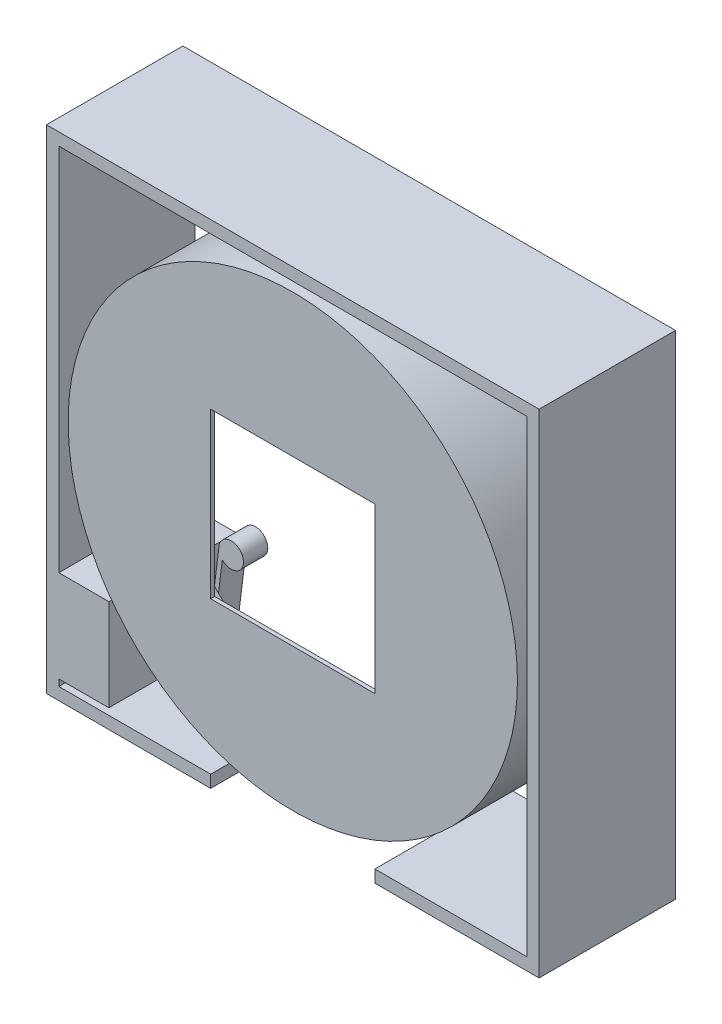
SolidWorks part; units mm, degrees
ref_plane "Front Plane" through (0, 0, 0) normal (0, 0, 1) x (1, 0, 0)
ref_plane "Top Plane" through (0, 0, 0) normal (0, 1, 0) x (1, 0, 0)
ref_plane "Right Plane" through (0, 0, 0) normal (1, 0, 0) x (0, 0, -1)
sketch "Sketch2" plane through (0, 0, 0) normal (0, 1, 0) x (1, 0, 0)
  line L0 (0, 0) -> (0, 14.0604) construction
  line L1 (0, 0) -> (43.434, 0)
  line L3 (0, 0) -> (0, 0.762)
  line L4 (43.434, 0) -> (43.434, 15.875)
  line L5 (0, 0.762) -> (42.672, 0.762)
  line L6 (42.672, 0.762) -> (42.672, 15.875)
  line L7 (42.672, 15.875) -> (43.434, 15.875)
  dimension "D1" = 15.875
  dimension "D2" = 86.868
  dimension "D3" = 0.762
revolve "Revolve1" add sketch "Sketch2" angle 360 about L0
sketch "Sketch3" plane through (0, 0, -0.762) normal (0, 0, -1) x (-1, 0, 0)
  line L1 (-15.875, -15.875) -> (15.875, -15.875)
  line L2 (-15.875, -15.875) -> (-15.875, 15.875)
  line L3 (-15.875, 15.875) -> (15.875, 15.875)
  line L4 (15.875, -15.875) -> (15.875, 15.875)
  line L5 (-15.875, -15.875) -> (15.875, 15.875) construction
  line L6 (-15.875, 15.875) -> (15.875, -15.875) construction
  point P0 (0, 0)
  dimension "D1" = 31.75
extrude "Cut-Extrude1" cut sketch "Sketch3" against normal through all contours L3 L4 L1 L2
sketch "Sketch4" plane through (0, 0, -0.762) normal (0, 0, -1) x (-1, 0, 0)
  line L1 (-12.7, 0) -> (12.7, 0)
  line L2 (-12.7, 0) -> (-12.7, -50.8)
  line L3 (-12.7, -50.8) -> (12.7, -50.8)
  line L4 (12.7, 0) -> (12.7, -50.8)
  point P4 (0, 0)
  dimension "D1" = 25.4
  dimension "D2" = 50.8
extrude "Cut-Extrude2" cut sketch "Sketch4" along normal through all contours L4 L3 L2 L1
sketch "Sketch5" plane through (0, 0, 0) normal (0, 0, 1) x (1, 0, 0)
  line L0 (45.2438, 45.2437) -> (-45.2437, 45.2437)
  line L1 (47.625, -47.625) -> (15.875, -47.625)
  line L2 (47.625, -47.625) -> (47.625, 47.625)
  line L3 (47.625, 47.625) -> (-47.625, 47.625)
  line L4 (-47.625, -47.625) -> (-47.625, 47.625)
  line L5 (47.625, -47.625) -> (-47.625, 47.625) construction
  line L6 (47.625, 47.625) -> (-47.625, -47.625) construction
  line L7 (-45.2437, -45.2438) -> (-45.2437, 45.2437)
  line L8 (45.2438, -45.2437) -> (15.875, -45.2437)
  line L9 (45.2438, -45.2437) -> (45.2438, 45.2437)
  line L10 (15.875, -45.2437) -> (15.875, -47.625)
  line L11 (0, 0) -> (0, -47.625) construction
  line L12 (-15.875, -45.2438) -> (-15.875, -47.625)
  line L13 (-15.875, -47.625) -> (-47.625, -47.625)
  line L14 (47.625, -47.625) -> (-47.625, -47.625) construction
  line L15 (-15.875, -45.2438) -> (-45.2437, -45.2438)
  line L16 (45.2438, -45.2437) -> (-45.2437, -45.2438) construction
  point P0 (0, 0)
  dimension "D2" = 95.25
  dimension "D3" = 31.75
  dimension "D1" = 2.3813
extrude "Boss-Extrude2" add sketch "Sketch5" against normal blind 26.3769 separate body contours L3 L4 L13 L12 L15 L7 L0 L9 L8 L10 L1 L2
sketch "Sketch6" plane through (0, 0, -26.3769) normal (0, 0, -1) x (-1, 0, 0)
  line L0 (34.8297, -43.9738) -> (32.7659, -27.3581)
  line L1 (34.8297, -26.1938) -> (44.9897, -26.1938)
  line L2 (34.8297, -26.1938) -> (34.8297, -43.9738)
  line L3 (34.8297, -43.9738) -> (44.9897, -43.9738)
  line L4 (44.9897, -26.1938) -> (44.9897, -43.9738)
  line L5 (33.4368, -25.7013) -> (34.8297, -36.9158)
  line L6 (45.2437, -45.2438) -> (45.2437, 45.2437) construction
  line L7 (15.875, -45.2438) -> (45.2437, -45.2438) construction
  circle A0 centre (31.0555, -25.7013) radius 2.3812
  dimension "D4" = 4.7625
  dimension "D1" = 17.78
  dimension "D2" = 10.16
  dimension "D3" = 0.87
  dimension "D5" = 0.254
  dimension "D6" = 1.27
extrude "Boss-Extrude3" add sketch "Sketch6" against normal blind 4.699 from offset 2.54 separate body contours L4 L1 L2 L3 | A0 | A0 L0 L2 L5 offset against normal yes
sketch "Sketch7" plane through (0, 0, -19.1379) normal (0, 0, 1) x (1, 0, 0)
  line L0 (-45.2437, -45.2438) -> (-45.2437, 45.2437) construction
  line L1 (-45.2437, -26.1938) -> (-35.5662, -26.1938)
  line L2 (-45.2437, -26.1938) -> (-45.2437, -43.9738)
  line L3 (-45.2437, -43.9738) -> (-35.5662, -43.9738)
  line L4 (-35.5662, -26.1938) -> (-35.5662, -43.9738)
  line L5 (-34.8297, -43.9738) -> (-44.9897, -43.9738) construction
  line L6 (-34.8297, -26.1938) -> (-44.9897, -26.1938) construction
extrude "Boss-Extrude4" add sketch "Sketch7" along normal up to surface (19.1379 mm away) up to face at (0, -15.4781, 0)
